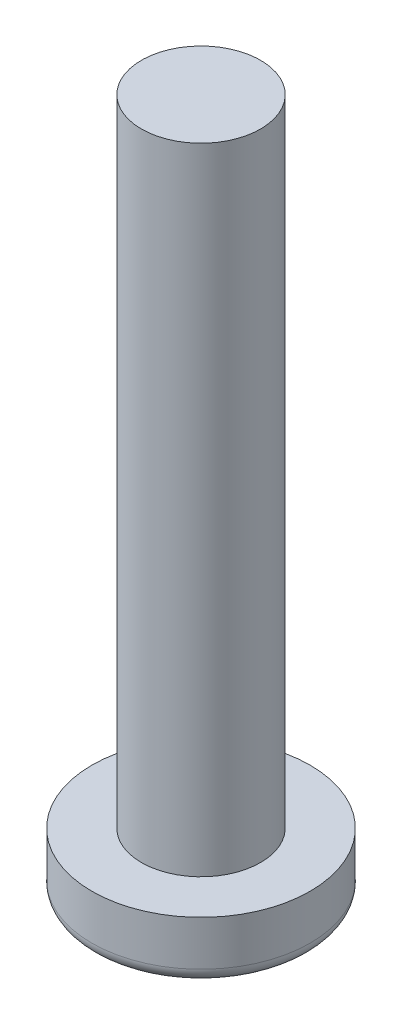
SolidWorks part; units mm, degrees
ref_plane "前视基准面" through (0, 0, 0) normal (0, 0, 1) x (1, 0, 0)
ref_plane "上视基准面" through (0, 0, 0) normal (0, 1, 0) x (1, 0, 0)
ref_plane "右视基准面" through (0, 0, 0) normal (1, 0, 0) x (0, 0, -1)
ref_plane "基准面4" through (0, 0, 15) normal (0, 0, 1) x (1, 0, 0)
sketch "草图1" plane through (0, 0, 15) normal (0, 0, 1) x (1, 0, 0)
  line L0 (2.75, 1.5) -> (0, 1.5)
  line L1 (0, 1.5) -> (0, 0)
  line L2 (0, 0) -> (2.75, 0)
  line L3 (2.75, 0) -> (2.75, 1.5)
  line L4 (0, 1.5) -> (0, 0) construction
revolve "旋转1" add sketch "草图1" angle 360 about L4
sketch "草图2" plane through (0, 1.5, 0) normal (0, 1, 0) x (-1, 0, 0)
  circle A0 centre (0, 15) radius 1.5
extrude "凸台-拉伸1" add sketch "草图2" along normal blind 16
fillet "圆角1" radius 0.3673 1 edges at (0, 0, 12.25)
